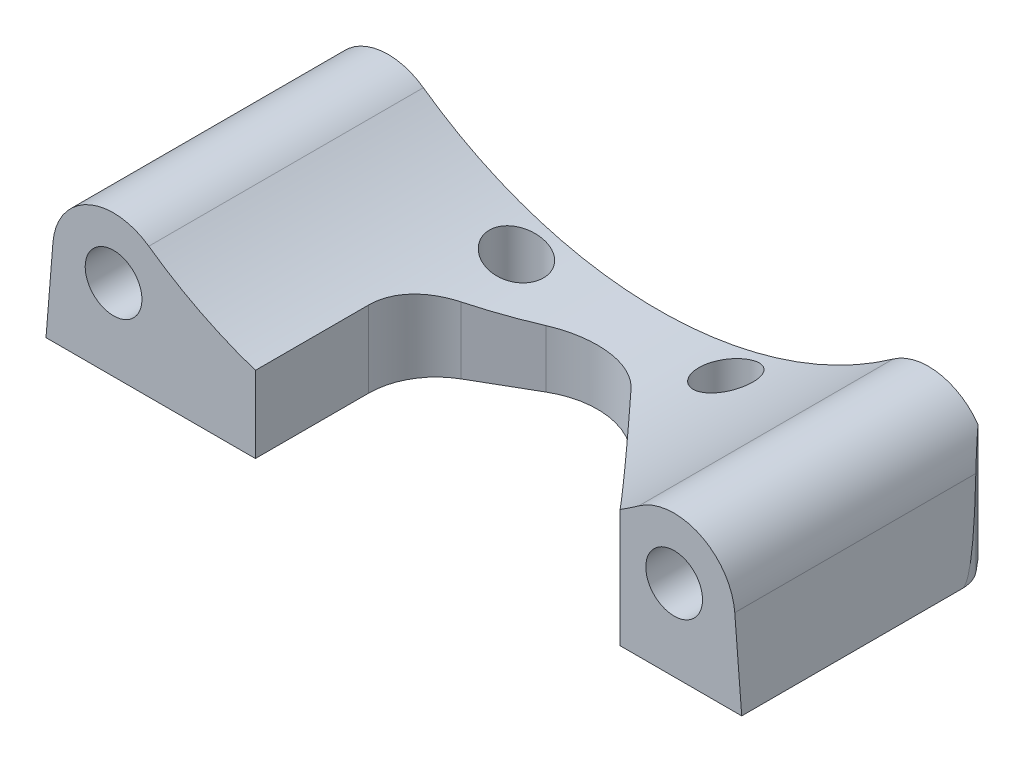
SolidWorks part; units mm, degrees
ref_plane "Front Plane" through (0, 0, 0) normal (0, 0, 1) x (1, 0, 0)
ref_plane "Top Plane" through (0, 0, 0) normal (0, 1, 0) x (1, 0, 0)
ref_plane "Right Plane" through (0, 0, 0) normal (1, 0, 0) x (0, 0, -1)
sketch "Sketch1" plane through (0, 0, 0) normal (0, 0, 1) x (1, 0, 0)
  line L0 (-48.9707, 12.7256) -> (-50, 0)
  line L1 (-50, 0) -> (50, 0)
  line L2 (50, 0) -> (48.9707, 12.7256)
  line L3 (-40, 12) -> (40, 12) construction
  line L4 (0, 12) -> (0, 0) construction
  circle A0 centre (-40, 12) radius 4.2
  circle A1 centre (40, 12) radius 4.2
  arc A2 (-34.7826, 19.3334) -> (-48.9707, 12.7256) centre (-40, 12) ccw
  arc A3 (48.9707, 12.7256) -> (34.7826, 19.3334) centre (40, 12) ccw
  arc A4 (-34.7826, 19.3334) -> (34.7826, 19.3334) centre (0, 68.2228) ccw
  dimension "D4" = 8.4
  dimension "D5" = 18
  dimension "D6" = 60
  dimension "D1" = 12
  dimension "D2" = 100
  dimension "D3" = 80
extrude "Boss-Extrude1" add sketch "Sketch1" along normal blind 40.65
sketch "Sketch2" plane through (0, 0, 0) normal (0, 0, -1) x (-1, 0, 0)
  circle A0 centre (-40, 12) radius 4.2 construction
  circle A1 centre (40, 12) radius 4.2 construction
  circle A2 centre (-40, 12) radius 4.2
  circle A3 centre (40, 12) radius 4.2
extrude "Boss-Extrude2" add sketch "Sketch2" against normal blind 18
sketch "Sketch3" plane through (0, 0, 0) normal (0, -1, 0) x (1, 0, 0)
  line L0 (50, 40.65) -> (50, 0) construction
  line L1 (-50, 0) -> (50, 0) construction
  line L2 (8.7647, 12.8036) -> (32, 37.65)
  line L3 (34.7826, 40.65) -> (-34.7826, 40.65) construction
  line L4 (50, 40.65) -> (-19, 40.65)
  line L5 (-19, 40.65) -> (-19, 23.8868)
  line L6 (-50, 40.65) -> (-50, 0) construction
  line L7 (32, 37.65) -> (50, 37.65)
  line L8 (-14, 15.2265) -> (-6, 10.6077)
  line L9 (50, 37.65) -> (50, 40.65)
  arc A0 (-6, 10.6077) -> (8.7647, 12.8036) centre (0, 21) ccw
  circle A1 centre (-15.5, 5.5) radius 4
  circle A2 centre (15.5, 5.5) radius 4
  circle A3 centre (-15.5, 36.5) radius 4 construction
  arc A4 (-14, 15.2265) -> (-19, 23.8868) centre (-9, 23.8868) cw
  dimension "D2" = 24
  dimension "D7" = 8
  dimension "D11" = 30
  dimension "D12" = 10
  dimension "D1" = 21
  dimension "D3" = 50
  dimension "D4" = 31
  dimension "D5" = 15.5
  dimension "D6" = 15.5
  dimension "D8" = 3
  dimension "D9" = 31
  dimension "D10" = 15.5
  dimension "D13" = 18
extrude "Cut-Extrude1" cut sketch "Sketch3" against normal through all
sketch "Sketch4" plane through (0, 0, 0) normal (0, -1, 0) x (1, 0, 0)
  line L0 (-50, 40.65) -> (-19, 40.65) construction
  line L1 (-50, 0) -> (50, 0) construction
  line L2 (-50, 40.65) -> (-50, 0) construction
  line L3 (50, 37.65) -> (50, 0) construction
  circle A0 centre (-32, 27.65) radius 2.6
  circle A1 centre (-45, 5) radius 2.6
  circle A2 centre (32, 27.65) radius 2.6
  circle A3 centre (45, 5) radius 2.6
  dimension "D3" = 5.2
  dimension "D1" = 13
  dimension "D2" = 5
  dimension "D4" = 18
  dimension "D5" = 18
  dimension "D6" = 5
  dimension "D7" = 5
extrude "Cut-Extrude2" cut sketch "Sketch4" against normal blind 6
chamfer "Chamfer1" distance 1 angle 45 4 edges at (34.6, 0, 27.65) (47.6, 0, 5) (-42.4, 0, 5) (-29.4, 0, 27.65)
sketch "Sketch5" plane through (0, 0, 0) normal (0, -1, 0) x (1, 0, 0)
  line L0 (-50, 5) -> (-50, 0)
  line L1 (-50, 0) -> (-47.3315, 0)
  line L2 (-50, 0) -> (50, 0) construction
  line L3 (-47.3315, 0) -> (-48.8302, 1.7861)
  line L4 (48.8302, 1.7861) -> (47.3315, 0)
  line L5 (47.3315, 0) -> (50, 0)
  line L6 (50, 0) -> (50, 5)
  arc A0 (-50, 5) -> (-48.8302, 1.7861) centre (-45, 5) ccw
  arc A1 (48.8302, 1.7861) -> (50, 5) centre (45, 5) ccw
  dimension "D1" = 40
  dimension "D2" = 40
extrude "Cut-Extrude3" cut sketch "Sketch5" against normal through all
